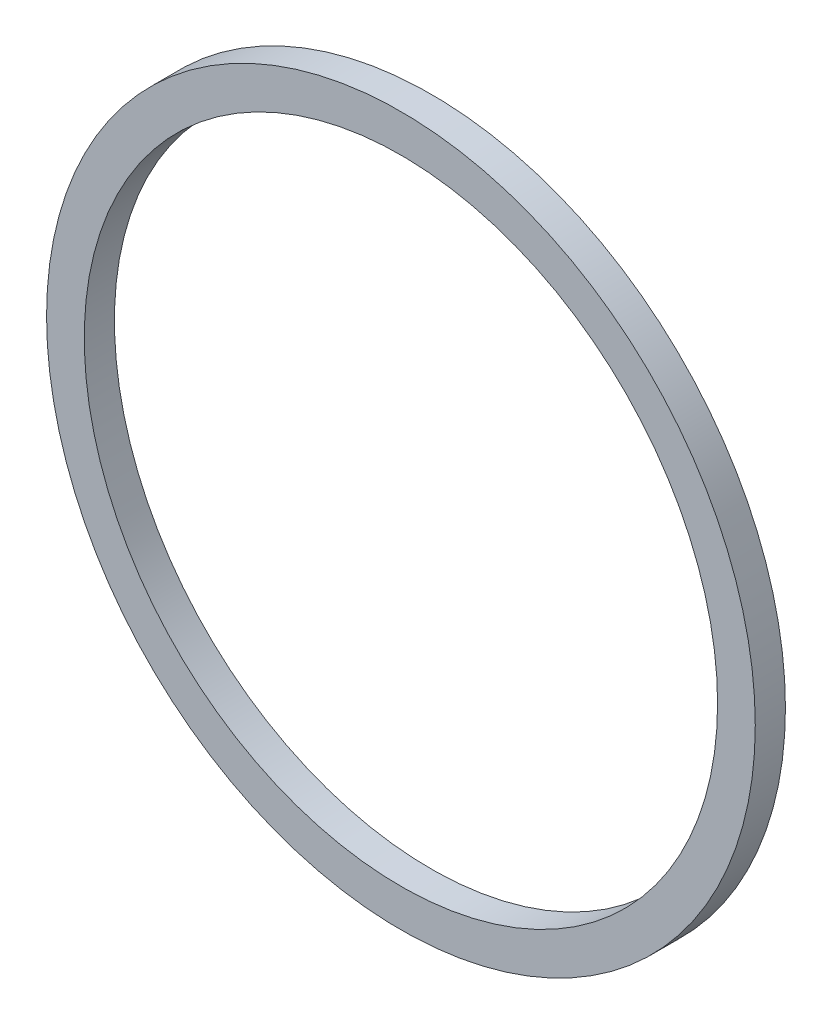
SolidWorks part; units mm, degrees
material "Thornel Mat VMA"
ref_plane "前视基准面" through (0, 0, 0) normal (0, 0, 1) x (1, 0, 0)
ref_plane "上视基准面" through (0, 0, 0) normal (0, 1, 0) x (1, 0, 0)
ref_plane "右视基准面" through (0, 0, 0) normal (1, 0, 0) x (0, 0, -1)
sketch "草图1" plane through (0, 0, 0) normal (0, 0, 1) x (1, 0, 0)
  circle A0 centre (0, 0) radius 21
  circle A1 centre (0, 0) radius 23.5
  dimension "D1" = 42
  dimension "D2" = 47
extrude "凸台-拉伸1" add sketch "草图1" along normal blind 2
